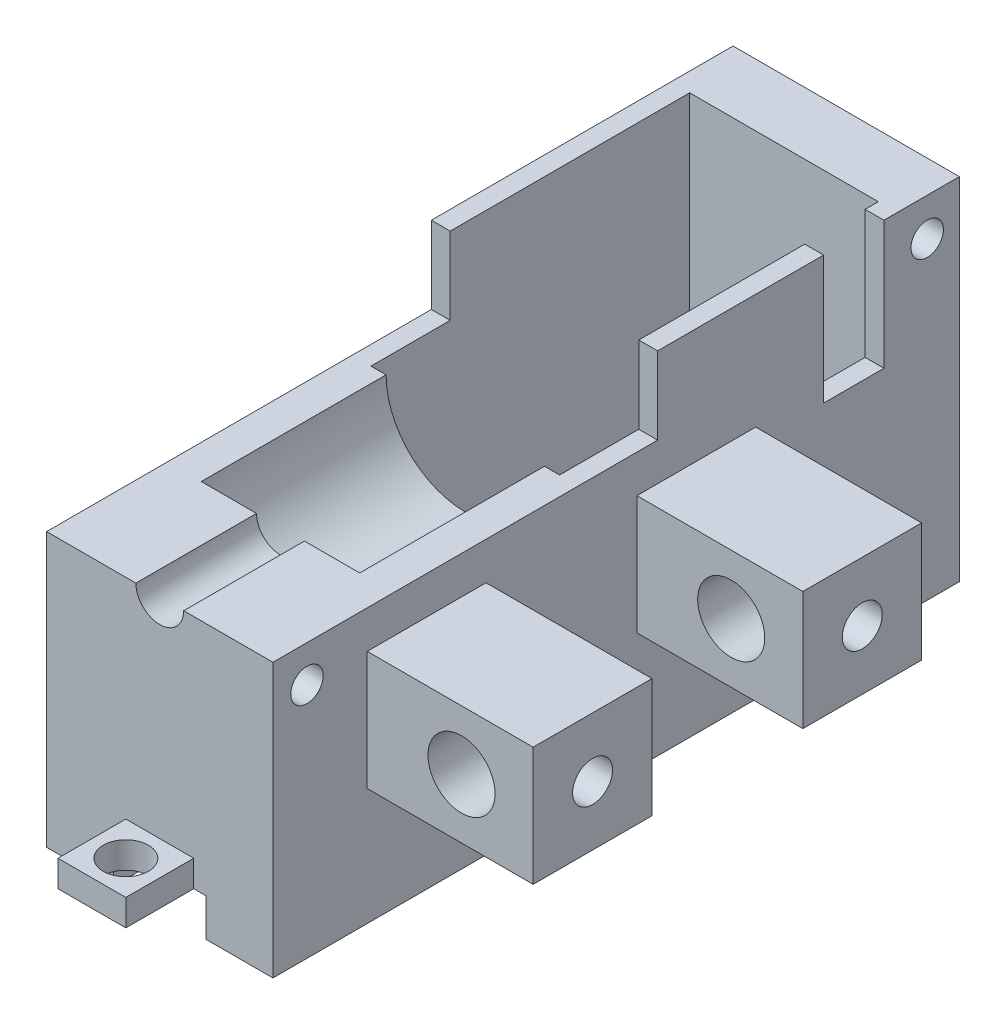
SolidWorks part; units mm, degrees
ref_plane "Front Plane" through (0, 0, 0) normal (0, 0, 1) x (1, 0, 0)
ref_plane "Top Plane" through (0, 0, 0) normal (0, 1, 0) x (1, 0, 0)
ref_plane "Right Plane" through (0, 0, 0) normal (1, 0, 0) x (0, 0, -1)
sketch "Sketch1" plane through (0, 0, 0) normal (0, 0, 1) x (1, 0, 0)
  line L1 (0, 0) -> (30, 0)
  line L2 (0, 0) -> (0, 41.5)
  line L3 (0, 41.5) -> (30, 41.5)
  line L4 (30, 0) -> (30, 41.5)
  dimension "D1" = 41.5
  dimension "D2" = 30
extrude "Boss-Extrude1" add sketch "Sketch1" along normal blind 40
sketch "Sketch2" plane through (0, 41.5, 0) normal (0, 1, 0) x (1, 0, 0)
  line L1 (2.5, -8.25) -> (27.5, -8.25)
  line L2 (2.5, -8.25) -> (2.5, -37.25)
  line L3 (2.5, -37.25) -> (27.5, -37.25)
  line L4 (27.5, -8.25) -> (27.5, -37.25)
  line L5 (0, -40) -> (0, 0) construction
  line L6 (30, -40) -> (0, -40) construction
  dimension "D1" = 29
  dimension "D2" = 25
  dimension "D3" = 2.5
  dimension "D4" = 2.75
extrude "Cut-Extrude1" cut sketch "Sketch2" against normal blind 35.5
sketch "Sketch3" plane through (0, 0, 37.25) normal (0, 0, -1) x (-1, 0, 0)
  line L0 (-27.5, 23.75) -> (-2.5, 23.75) construction
  line L1 (-27.5, 6) -> (-27.5, 41.5) construction
  line L2 (-2.5, 6) -> (-2.5, 41.5) construction
  line L3 (-15, 41.5) -> (-15, 6) construction
  line L4 (-2.5, 41.5) -> (-27.5, 41.5) construction
  line L5 (-2.5, 6) -> (-27.5, 6) construction
  line L7 (-23.5, 23.75) -> (-6.5, 23.75)
  line L8 (-23.5, 23.75) -> (-23.5, 36.5)
  line L9 (-23.5, 36.5) -> (-6.5, 36.5)
  line L10 (-6.5, 23.75) -> (-6.5, 36.5)
  line L11 (-30, 41.5) -> (0, 41.5) construction
  line L12 (-23.5, 36.5) -> (-6.5, 36.5)
  line L13 (-23.5, 36.5) -> (-23.5, 41.5)
  line L14 (-23.5, 41.5) -> (-6.5, 41.5)
  line L15 (-6.5, 36.5) -> (-6.5, 41.5)
  circle A0 centre (-15, 23.75) radius 8.5
  line M2 (-2.5, 41.5) -> (-27.5, 41.5)
  dimension "D1" = 17
  dimension "D2" = 0
  dimension "D3" = 0
  dimension "D4" = 5
extrude "Cut-Extrude2" cut sketch "Sketch3" against normal blind 19 contours A0 L9 L8 | L7 A0 L12 | L12 A0 | L7 A0 | A0 L10 L9 | A0 L15 L13 M2
sketch "Sketch4" [suppressed] plane through (0, 0, 37.25) normal (0, 0, -1) x (-1, 0, 0)
  line L0 (-24.75, 38.85) -> (-9.25, 38.85) construction
  line L2 (0, 41.5) -> (0, 0) construction
  line L3 (-23.5, 41.5) -> (-27.5, 41.5) construction
  line L4 (-30, 0) -> (-30, 41.5) construction
  dimension "D1" = 5.25
  dimension "D2" = 15.5
  dimension "D3" = 2.65
  dimension "D4" = 9.25
sketch "Sketch7" plane through (0, 0, 0) normal (0, -1, 0) x (1, 0, 0)
  line L0 (0, 0) -> (30, 0) construction
  line L1 (10.5, 0) -> (19.5, 0)
  line L2 (10.5, 0) -> (10.5, -9)
  line L3 (10.5, -9) -> (19.5, -9)
  line L4 (19.5, 0) -> (19.5, -9)
  line L5 (0, 40) -> (0, 0) construction
  line L6 (30, 40) -> (30, 0) construction
  dimension "D1" = 9
  dimension "D2" = 10.5
  dimension "D3" = 10.5
  dimension "D4" = 9
extrude "Boss-Extrude2" add sketch "Sketch7" against normal blind 3.5
sketch "Sketch8" plane through (0, 3.5, 0) normal (0, 1, 0) x (1, 0, 0)
  line L0 (10.5, 4.5) -> (19.5, 4.5) construction
  line L1 (10.5, 0) -> (10.5, 9) construction
  line L2 (19.5, 9) -> (19.5, 0) construction
  line L3 (15, 9) -> (15, 0) construction
  line L4 (10.5, 9) -> (19.5, 9) construction
  line L5 (30, 0) -> (0, 0) construction
  circle A0 centre (15, 4.5) radius 3
  dimension "D1" = 6
extrude "Cut-Extrude3" cut sketch "Sketch8" against normal blind 7
sketch "Sketch9" plane through (0, 0, 40) normal (0, 0, 1) x (1, 0, 0)
  line L0 (0, 0) -> (0, 31.25)
  line L1 (0, 41.5) -> (0, 0) construction
  line L2 (4.5, 31.25) -> (0, 31.25)
  line L3 (25.5, 31.25) -> (30, 31.25)
  line L4 (30, 0) -> (30, 41.5) construction
  line L5 (30, 31.25) -> (30, 0)
  line L6 (30, 0) -> (0, 0)
  arc A0 (4.5, 31.25) -> (25.5, 31.25) centre (15, 31.25) ccw
  dimension "D1" = 10.5
  dimension "D2" = 4.5
  dimension "D3" = 31.25
extrude "Boss-Extrude3" add sketch "Sketch9" along normal blind 35
sketch "Sketch10" plane through (0, 0, 75) normal (0, 0, 1) x (1, 0, 0)
  line L1 (0, 0) -> (30, 0)
  line L2 (0, 0) -> (0, 31.25)
  line L3 (0, 31.25) -> (30, 31.25)
  line L4 (30, 0) -> (30, 31.25)
extrude "Boss-Extrude4" add sketch "Sketch10" along normal blind 16
ref_plane "Plane1" through (0, 0, 45.5) normal (0, 0, 1) x (1, 0, 0)
mirror "Mirror1" about plane through (0, 0, 45.5) normal (0, 0, 1) of "Boss-Extrude2", "Cut-Extrude3"
sketch "Sketch11" plane through (0, 0, 91) normal (0, 0, 1) x (1, 0, 0)
  line L0 (30, 31.25) -> (0, 31.25) construction
  line L1 (11.825, 31.25) -> (18.175, 31.25)
  arc A0 (18.175, 31.25) -> (11.825, 31.25) centre (15, 31.25) cw
  dimension "D1" = 3.175
extrude "Cut-Extrude4" cut sketch "Sketch11" against normal blind 25
sketch "Sketch12" plane through (30, 0, 0) normal (-1, 0, 0) x (0, 0, 1)
  line L0 (40, 41.5) -> (0, 41.5) construction
  line L1 (10, 41.5) -> (18, 41.5)
  line L2 (10, 41.5) -> (10, 24.5)
  line L3 (10, 24.5) -> (18, 24.5)
  line L4 (18, 41.5) -> (18, 24.5)
  line L5 (0, 41.5) -> (0, 0) construction
  dimension "D1" = 10
  dimension "D2" = 17
  dimension "D3" = 8
extrude "Cut-Extrude5" cut sketch "Sketch12" against normal up to surface (27.5 mm away)
sketch "Sketch13" plane through (0, 0, 0) normal (-1, 0, 0) x (0, 0, 1)
  line L0 (4.266, 41.5) -> (4.266, 36.5) construction
  line L1 (40, 41.5) -> (0, 41.5) construction
  circle A0 centre (4.266, 36.5) radius 2.15
  dimension "D2" = 4.3
  dimension "D1" = 5
extrude "Cut-Extrude6" cut sketch "Sketch13" against normal blind 10
sketch "Sketch14" plane through (30, 0, 65) normal (-1, 0, 0) x (0, 0, 1)
  line L0 (3.5318, 9.4488) -> (22.47, 9.4488) construction
  line L3 (26, 31.25) -> (26, 0) construction
  line L4 (26, 0) -> (26, 31.25) construction
  dimension "D1" = 22.4682
  dimension "D2" = 3.53
ref_plane "Plane2" through (15, 0, 0) normal (1, 0, 0) x (0, 0, -1)
mirror "Mirror2" about plane through (15, 0, 0) normal (1, 0, 0) of "Cut-Extrude6"
sketch "Sketch17" plane through (30, 0, 0) normal (1, 0, 0) x (0, 0, -1)
  line L1 (-78.5, 26.25) -> (-62.75, 26.25)
  line L2 (-78.5, 26.25) -> (-78.5, 10.5)
  line L3 (-78.5, 10.5) -> (-62.75, 10.5)
  line L4 (-62.75, 26.25) -> (-62.75, 10.5)
  line L7 (-42.75, 26.25) -> (-27, 26.25)
  line L8 (-42.75, 26.25) -> (-42.75, 10.5)
  line L9 (-42.75, 10.5) -> (-27, 10.5)
  line L10 (-27, 26.25) -> (-27, 10.5)
  line L12 (-91, 31.25) -> (-40, 31.25) construction
  dimension "D1" = 12.5
  dimension "D2" = 20
  dimension "D3" = 15.75
  dimension "D4" = 5
extrude "Boss-Extrude5" add sketch "Sketch17" along normal blind 22
sketch "Sketch18" plane through (0, 0, 78.5) normal (0, 0, 1) x (1, 0, 0)
  line L0 (52, 26.25) -> (52, 10.5) construction
  line L1 (52, 10.5) -> (30, 10.5) construction
  line L2 (52, 26.25) -> (30, 26.25) construction
  circle A0 centre (42.5, 18.375) radius 4.445
  dimension "D1" = 8.89
  dimension "D2" = 9.5
  dimension "D3" = 7.875
  dimension "D4" = 7.875
extrude "Cut-Extrude7" cut sketch "Sketch18" against normal blind 62.75
sketch "Sketch19" plane through (30, 0, 0) normal (1, 0, 0) x (0, 0, -1)
  circle A0 centre (-86.4865, 26.3957) radius 2.15
  dimension "D1" = 4.3
extrude "Cut-Extrude8" cut sketch "Sketch19" against normal blind 5
ref_plane "Plane3" through (52, 26.25, 62.75) normal (0, 0, 1) x (1, 0, 0)
sketch "Sketch21" plane through (0, 0, 0) normal (-1, 0, 0) x (0, 0, 1)
  circle A0 centre (86.4865, 26.3957) radius 2.15
  dimension "D1" = 4.3
extrude "Cut-Extrude9" cut sketch "Sketch21" against normal blind 5
sketch "Sketch22" [suppressed] plane through (0, 0, 0) normal (0, 0, 1) x (-1, 0, 0)
  line L1 (-7, 238) -> (-0.25, 238)
  line L2 (-7, 238) -> (-7, 147)
  line L3 (-7, 147) -> (-0.25, 147)
  line L4 (-0.25, 238) -> (-0.25, 147)
  line L5 (12.25, 147) -> (19, 147)
  line L6 (12.25, 147) -> (12.25, 238)
  line L7 (12.25, 238) -> (19, 238)
  line L8 (19, 147) -> (19, 238)
  dimension "D1" = 6.75
  dimension "D2" = 6.75
sketch "Sketch23" plane through (0, 0, 0) normal (0, -1, 0) x (-1, 0, 0)
  line L0 (-19.5, -91) -> (-30, -91) construction
  line L1 (-30, 0) -> (-21.125, 0)
  line L2 (-30, 0) -> (-30, -91)
  line L3 (-30, -91) -> (-21.125, -91)
  line L4 (-21.125, 0) -> (-21.125, -91)
  line L5 (0, 0) -> (-10.5, 0) construction
  line L6 (0, -91) -> (-8.875, -91)
  line L7 (0, -91) -> (0, 0)
  line L8 (0, 0) -> (-8.875, 0)
  line L9 (-8.875, -91) -> (-8.875, 0)
  dimension "D1" = 8.875
  dimension "D2" = 8.875
extrude "Boss-Extrude6" add sketch "Sketch23" along normal blind 5
sketch "Sketch24" plane through (52, 0, 0) normal (1, 0, 0) x (0, 0, -1)
  line L0 (-78.5, 18.375) -> (-62.75, 18.375)
  line L1 (-78.5, 26.25) -> (-78.5, 10.5) construction
  line L2 (-62.75, 10.5) -> (-62.75, 26.25) construction
  line L3 (-42.75, 18.375) -> (-27, 18.375)
  line L4 (-42.75, 26.25) -> (-42.75, 10.5) construction
  line L5 (-27, 10.5) -> (-27, 26.25) construction
  circle A0 centre (-70.625, 18.375) radius 2.65
  circle A1 centre (-34.875, 18.375) radius 2.65
  dimension "D1" = 5.3
extrude "Cut-Extrude10" cut sketch "Sketch24" against normal up to surface (5.055 mm away) contours L0 A0 | L3 A1 | L3 A1 | L0 A0 up to face at (46.945, 18.375, 78.5)
sketch "Sketch25" plane through (0, 6, 0) normal (0, 1, 0) x (1, 0, 0)
  line L0 (15, -40) -> (15, -31)
  line L1 (27.5, -40) -> (2.5, -40) construction
  line L2 (15, -22.825) -> (15, 22.825) construction
  line L3 (15, -31) -> (15, -16)
  circle A0 centre (15, -16) radius 2.15
  circle A1 centre (15, -31) radius 2.15
  dimension "D1" = 4.3
  dimension "D2" = 4.3
  dimension "D3" = 9
  dimension "D4" = 15
extrude "Cut-Extrude11" cut sketch "Sketch25" against normal through all
sketch "Sketch26" plane through (0, 31.25, 0) normal (0, 1, 0) x (1, 0, 0)
  line L0 (27.5, -40) -> (27.5, -8.25) construction
  line L1 (2.5, -40) -> (27.5, -40)
  line L2 (2.5, -40) -> (2.5, -42.5)
  line L3 (2.5, -42.5) -> (27.5, -42.5)
  line L4 (27.5, -40) -> (27.5, -42.5)
  dimension "D1" = 0
  dimension "D2" = 2.5
extrude "Cut-Extrude12" cut sketch "Sketch26" against normal up to surface (25.25 mm away) up to face at (15, 6, 33.15)
sketch "Sketch27" plane through (0, 31.25, 0) normal (0, 1, 0) x (1, 0, 0)
  line L0 (27.5, -40) -> (27.5, -18) construction
  line L1 (2.5, -42.5) -> (27.5, -42.5)
  line L2 (2.5, -42.5) -> (2.5, -50.5)
  line L3 (2.5, -50.5) -> (27.5, -50.5)
  line L4 (27.5, -42.5) -> (27.5, -50.5)
  dimension "D1" = 0
  dimension "D2" = 8
extrude "Cut-Extrude13" cut sketch "Sketch27" against normal up to surface (25.25 mm away) up to face at (15, 6, 33.15)
